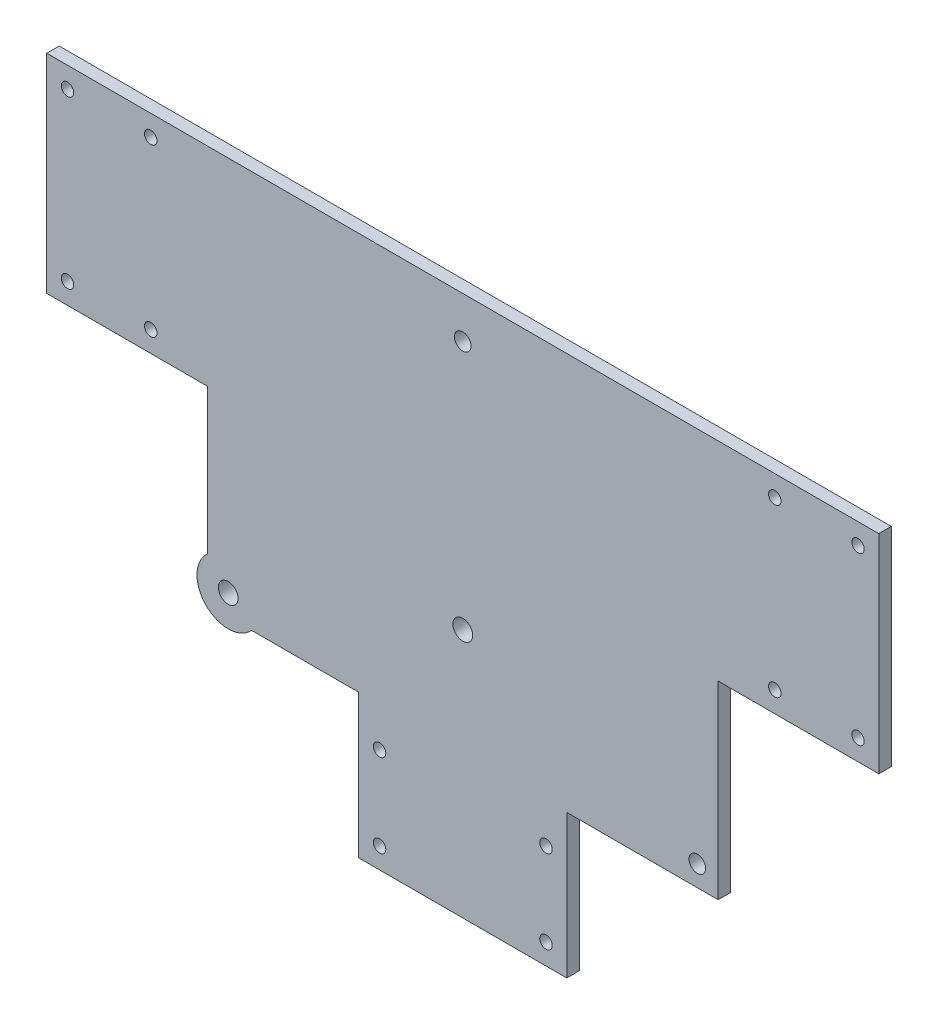
SolidWorks part; units mm, degrees
ref_plane "Plan de face" through (0, 0, 0) normal (0, 0, 1) x (1, 0, 0)
ref_plane "Plan de dessus" through (0, 0, 0) normal (0, 1, 0) x (1, 0, 0)
ref_plane "Plan de droite" through (0, 0, 0) normal (1, 0, 0) x (0, 0, -1)
sketch "Esquisse1" plane through (0, 0, 0) normal (0, 0, 1) x (1, 0, 0)
  line L0 (-25, 0) -> (25, 0) construction
  line L1 (0, 50) -> (-100, 50)
  line L2 (25, -80) -> (25, -45.5212)
  line L3 (-70, 50) -> (-70, 0) construction
  line L4 (25, -80) -> (-25, -80)
  line L5 (-25, -50) -> (25, -50) construction
  line L6 (-25, -65) -> (25, -65) construction
  line L7 (-25, -80) -> (-25, -45.5212)
  line L8 (0, 50) -> (0, -80) construction
  line L9 (-85, 50) -> (-85, 0) construction
  line L10 (0, 50) -> (100, 50)
  line L11 (100, 50) -> (100, 0)
  line L12 (100, 0) -> (61.3816, 0)
  line L13 (-100, 50) -> (-100, 0)
  line L14 (-100, 0) -> (-61.3816, 0)
  line L15 (61.3816, 0) -> (25, 0) construction
  line L16 (-100, 25) -> (-70, 25) construction
  line L17 (-25, -45.5212) -> (-25, 0) construction
  line L18 (-61.3816, 0) -> (-61.3816, -45.5212)
  line L19 (-61.3816, -45.5212) -> (-25, -45.5212)
  line L20 (0, -20) -> (-25, -20) construction
  line L21 (25, -45.5212) -> (25, 0) construction
  line L22 (61.3816, 0) -> (61.3816, -45.5212)
  line L23 (61.3816, -45.5212) -> (25, -45.5212)
  line L24 (0, -20) -> (-56.3816, -40.5212) construction
  circle A0 centre (0, 20) radius 2
  circle A1 centre (0, -20) radius 2
  circle A2 centre (0, 40) radius 2
  circle A3 centre (-20, -55) radius 1.5
  circle A4 centre (20, -55) radius 1.5
  circle A5 centre (20, -75) radius 1.5
  circle A6 centre (-20, -75) radius 1.5
  circle A7 centre (-95, 45) radius 1.5
  circle A8 centre (-75, 45) radius 1.5
  circle A9 centre (-75, 5) radius 1.5
  circle A10 centre (-95, 5) radius 1.5
  circle A11 centre (75, 5) radius 1.5
  circle A12 centre (95, 5) radius 1.5
  circle A13 centre (75, 45) radius 1.5
  circle A14 centre (95, 45) radius 1.5
  circle A15 centre (56.3816, -40.5212) radius 2
  circle A17 centre (-56.3816, -40.5212) radius 2
  point P0 (0, 0)
  point P2 (0, 0)
  dimension "D3" = 4
  dimension "D4" = 4
  dimension "D5" = 20
  dimension "D7" = 4
  dimension "D13" = 3
  dimension "D14" = 20
  dimension "D19" = 3
  dimension "D20" = 10
  dimension "D21" = 20
  dimension "D22" = 5
  dimension "D23" = 5
  dimension "D24" = 60
  dimension "D25" = 20
  dimension "D26" = 4
  dimension "D27" = 25
  dimension "D6" = 20
  dimension "D8" = 40
  dimension "D9" = 80
  dimension "D10" = 30
  dimension "D11" = 30
  dimension "D12" = 15
  dimension "D15" = 10
  dimension "D16" = 100
  dimension "D17" = 50
  dimension "D18" = 15
extrude "Boss.-Extru.1" add sketch "Esquisse1" along normal blind 3
sketch "Esquisse3" plane through (0, 0, 0) normal (0, 0, -1) x (-1, 0, 0)
  circle A0 centre (0, 20) radius 7.5
  circle A1 centre (56.3816, -40.5212) radius 7.5
  circle A2 centre (0, -20) radius 7.5
  dimension "D1" = 15
  dimension "D2" = 15
  dimension "D3" = 15
extrude "Boss.-Extru.2" add sketch "Esquisse3" along normal blind 6 from offset 3
sketch "Esquisse4" plane through (0, 0, -3) normal (0, 0, -1) x (-1, 0, 0)
  circle A0 centre (56.3816, -40.5212) radius 3.875
  circle A1 centre (0, 20) radius 3.875
  circle A2 centre (0, -20) radius 3.875
  dimension "D1" = 7.75
  dimension "D2" = 7.75
  dimension "D3" = 7.75
extrude "Enlèv. mat.-Extru.1" cut sketch "Esquisse4" against normal blind 1
sketch "Esquisse5" plane through (0, 0, -2) normal (0, 0, -1) x (-1, 0, 0)
  circle A0 centre (56.3816, -40.5212) radius 2.375
  circle A1 centre (0, 20) radius 2.375
  circle A2 centre (0, -20) radius 2.375
  dimension "D1" = 4.75
  dimension "D2" = 4.75
  dimension "D3" = 4.75
extrude "Enlèv. mat.-Extru.2" cut sketch "Esquisse5" against normal blind 4
sketch "Esquisse6" plane through (0, 0, 2) normal (0, 0, -1) x (-1, 0, 0)
  circle A0 centre (56.3816, -40.5212) radius 2.375
  circle A1 centre (0, -20) radius 2.375
extrude "Enlèv. mat.-Extru.3" cut sketch "Esquisse6" against normal up to next
